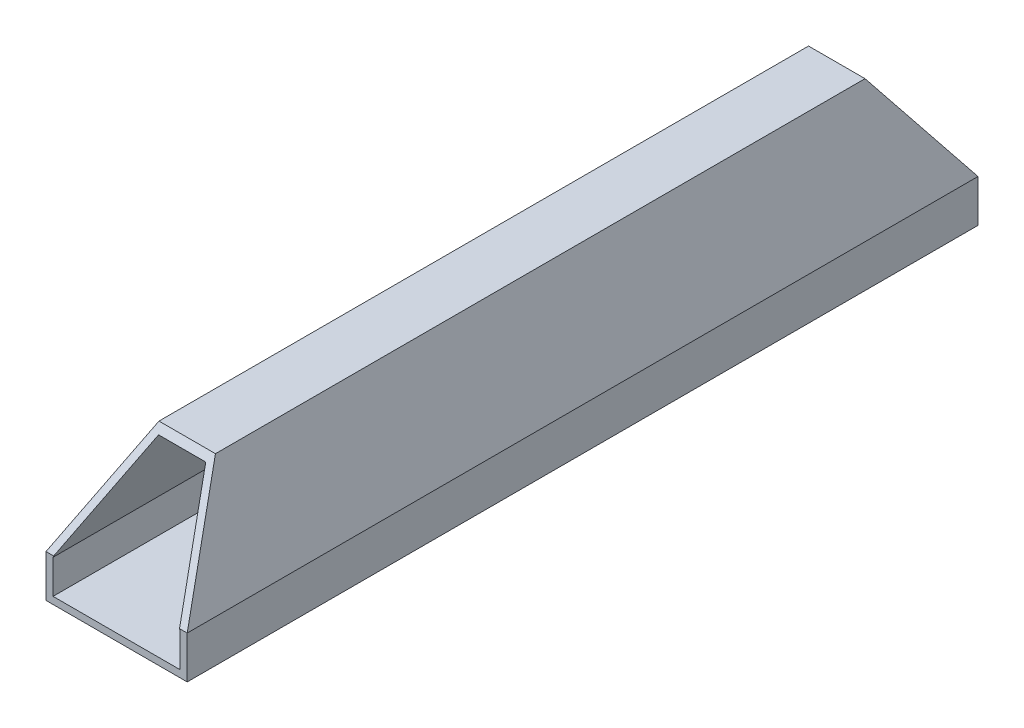
SolidWorks part; units mm, degrees
ref_plane "Front Plane" through (0, 0, 0) normal (0, 0, 1) x (1, 0, 0)
ref_plane "Top Plane" through (0, 0, 0) normal (0, 1, 0) x (1, 0, 0)
ref_plane "Right Plane" through (0, 0, 0) normal (1, 0, 0) x (0, 0, -1)
sketch "Sketch1" plane through (0, 0, 0) normal (0, 0, 1) x (1, 0, 0)
  line L0 (0, 14.7803) -> (0, -13.5318) construction
  line L1 (30.0733, 0) -> (-31.1041, 0) construction
  line L2 (-4, 14) -> (4, 14)
  line L3 (4, 14) -> (10, 0)
  line L4 (10, 0) -> (10, -6)
  line L5 (10, -6) -> (-10, -6)
  line L6 (-10, -6) -> (-10, 0)
  line L7 (-10, 0) -> (-4, 14)
  point P7 (0, -6)
  point P12 (0, 14)
  dimension "D1" = 20
  dimension "D2" = 20
  dimension "D3" = 8
  dimension "D4" = 6
extrude "Boss-Extrude1" add sketch "Sketch1" along normal blind 112
sketch "Sketch2" plane through (0, 0, 112) normal (0, 0, 1) x (1, 0, 0)
  line L12 (-3.3406, 13) -> (-9, -0.2053)
  line L13 (-9, -0.2053) -> (-9, -5)
  line L14 (-9, -5) -> (9, -5)
  line L15 (9, -5) -> (9, -0.2053)
  line L16 (9, -0.2053) -> (3.3406, 13)
  line L17 (3.3406, 13) -> (-3.3406, 13)
  line L18 (-3.3406, 13) -> (-9, -0.2053)
  line L19 (-9, -0.2053) -> (-9, -5)
  line L20 (-9, -5) -> (9, -5)
  line L21 (9, -5) -> (9, -0.2053)
  line L22 (9, -0.2053) -> (3.3406, 13)
  line L23 (3.3406, 13) -> (-3.3406, 13)
  dimension "D1" = 1
extrude "Cut-Extrude1" cut sketch "Sketch2" against normal through all
sketch "Sketch4" plane through (10, 0, 0) normal (1, 0, 0) x (0, 0, -1)
  line L0 (-112, 14) -> (-102, 14)
  line L1 (-112, 14) -> (0, 14) construction
  line L2 (-102, 14) -> (-112, 0)
  line L3 (-112, 0) -> (-112, 14)
  dimension "D1" = 10
  dimension "D2" = 14
extrude "Cut-Extrude2" cut sketch "Sketch4" against normal through all
sketch "Sketch5" plane through (-10, 0, 0) normal (-1, 0, 0) x (0, 0, 1)
  line L0 (0, 14) -> (10, 14)
  line L1 (102, 14) -> (0, 14) construction
  line L2 (10, 14) -> (0, 0)
  line L3 (0, 0) -> (0, 14)
  dimension "D1" = 14
  dimension "D2" = 10
extrude "Cut-Extrude3" cut sketch "Sketch5" against normal through all
